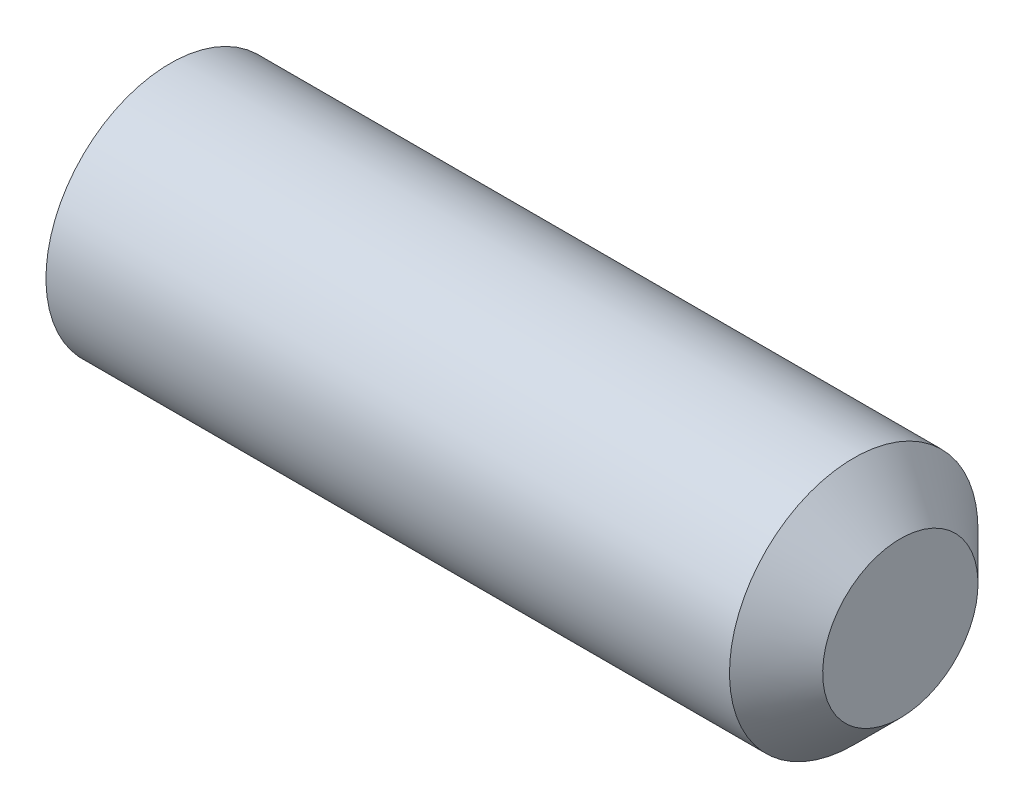
SolidWorks part; units mm, degrees
ref_plane "Front Plane" through (0, 0, 0) normal (0, 0, 1) x (1, 0, 0)
ref_plane "Top Plane" through (0, 0, 0) normal (0, 1, 0) x (1, 0, 0)
ref_plane "Right Plane" through (0, 0, 0) normal (1, 0, 0) x (0, 0, -1)
ref_plane "Plane1" through (0, 0, 0) normal (0, 0, 1) x (1, 0, 0)
sketch "Sketch1" plane through (0, 0, 0) normal (0, 0, 1) x (1, 0, 0)
  line L0 (12, 0) -> (12, -1.25)
  line L1 (12, -1.25) -> (11.25, -2)
  line L2 (11.25, -2) -> (0.248, -2)
  line L3 (0.248, -2) -> (0, -1.5705)
  line L4 (0, -1.5705) -> (0, -1.1547)
  line L5 (0, -1.1547) -> (0.6667, 0)
  line L6 (0.6667, 0) -> (12, 0)
  line L7 (0.6667, 0) -> (12, 0) construction
revolve "Revolve1" add sketch "Sketch1" angle 360 about L7
ref_plane "Plane2" through (0, 0, 0) normal (1, 0, 0) x (0, 0, -1)
sketch "Sketch2" plane through (0, 0, 0) normal (1, 0, 0) x (0, 0, -1)
  line L0 (-1.1547, 0) -> (-0.5774, -1)
  line L1 (-0.5774, -1) -> (0.5774, -1)
  line L2 (0.5774, -1) -> (1.1547, 0)
  line L3 (1.1547, 0) -> (0.5774, 1)
  line L4 (0.5774, 1) -> (-0.5774, 1)
  line L5 (-0.5774, 1) -> (-1.1547, 0)
extrude "Cut-Extrude1" cut sketch "Sketch2" along normal blind 2.5
